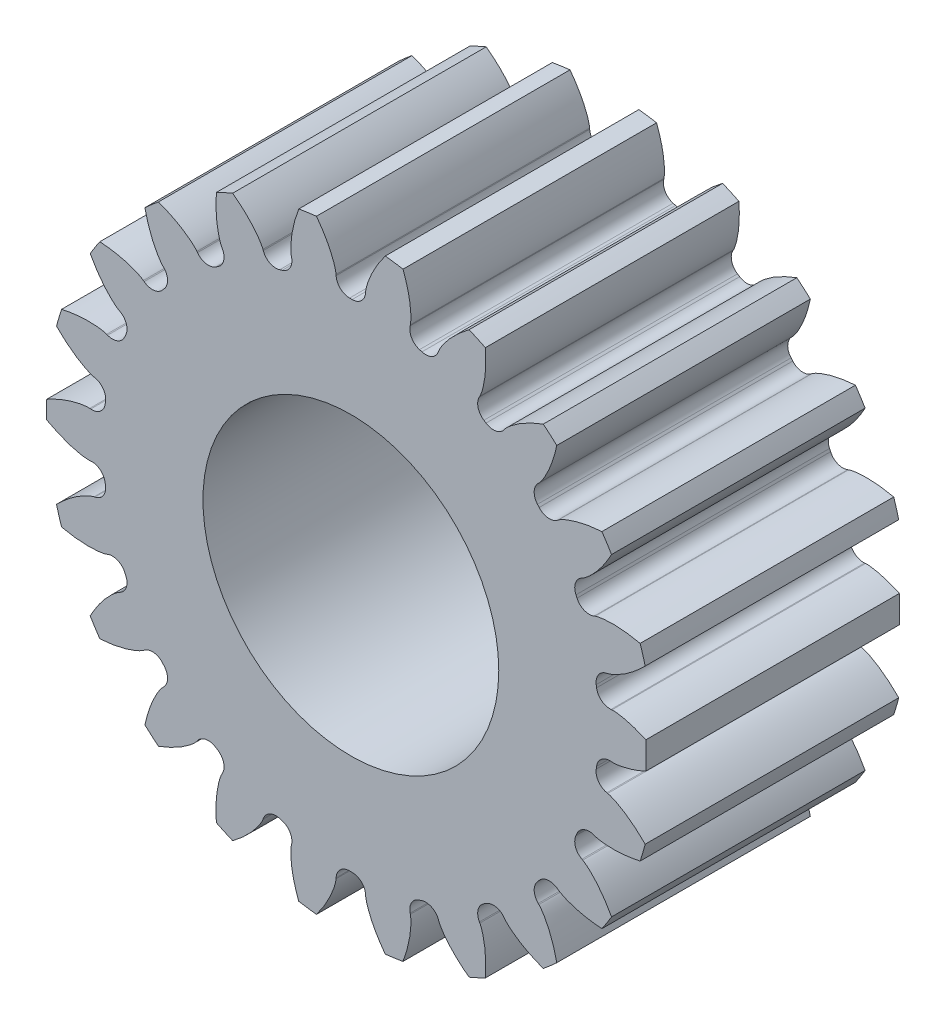
SolidWorks part; units mm, degrees
ref_plane "Front Plane" through (0, 0, 0) normal (0, 0, 1) x (1, 0, 0)
ref_plane "Top Plane" through (0, 0, 0) normal (0, 1, 0) x (1, 0, 0)
ref_plane "Right Plane" through (0, 0, 0) normal (1, 0, 0) x (0, 0, -1)
sketch "Sketch1" plane through (0, 0, 0) normal (0, 0, 1) x (1, 0, 0)
  circle A0 centre (-854.9, 935.5) radius 17.5
  line B0 (-820, 933.8919) -> (-820, 937.1081)
  line B1 (-824.0056, 938.173) -> (-824.1199, 938.1631)
  line B2 (-824.6164, 941.6165) -> (-824.5039, 941.6393)
  line B3 (-826.0101, 946.7687) -> (-826.117, 946.727)
  line B4 (-827.5663, 949.9006) -> (-827.4648, 949.9542)
  line B5 (-830.3551, 954.4514) -> (-830.4459, 954.3814)
  line B6 (-832.7306, 957.0181) -> (-832.6484, 957.098)
  line B7 (-836.6885, 960.5989) -> (-836.756, 960.506)
  line B8 (-839.691, 962.3923) -> (-839.6346, 962.4922)
  line B9 (-844.4974, 964.713) -> (-844.5359, 964.6049)
  line B10 (-847.8835, 965.5878) -> (-847.8575, 965.6996)
  line B11 (-853.149, 966.4604) -> (-853.1556, 966.3458)
  line B12 (-856.6444, 966.3458) -> (-856.651, 966.4604)
  line B13 (-861.9425, 965.6996) -> (-861.9165, 965.5878)
  line B14 (-865.2641, 964.6049) -> (-865.3026, 964.713)
  line B15 (-870.1654, 962.4922) -> (-870.109, 962.3923)
  line B16 (-873.044, 960.506) -> (-873.1115, 960.5989)
  line B17 (-877.1516, 957.098) -> (-877.0694, 957.0181)
  line B18 (-879.3541, 954.3814) -> (-879.4449, 954.4514)
  line B19 (-882.3352, 949.9542) -> (-882.2337, 949.9006)
  line B20 (-883.683, 946.727) -> (-883.7899, 946.7687)
  line B21 (-885.2961, 941.6393) -> (-885.1836, 941.6165)
  line B22 (-885.6801, 938.1631) -> (-885.7944, 938.173)
  line B23 (-885.7944, 932.827) -> (-885.6801, 932.8369)
  line B24 (-885.1836, 929.3835) -> (-885.2961, 929.3607)
  line B25 (-883.7899, 924.2313) -> (-883.683, 924.273)
  line B26 (-882.2337, 921.0994) -> (-882.3352, 921.0458)
  line B27 (-879.4449, 916.5486) -> (-879.3541, 916.6186)
  line B28 (-877.0694, 913.9819) -> (-877.1516, 913.902)
  line B29 (-873.1115, 910.4011) -> (-873.044, 910.494)
  line B30 (-870.109, 908.6077) -> (-870.1654, 908.5078)
  line B31 (-865.3026, 906.287) -> (-865.2641, 906.3951)
  line B32 (-861.9165, 905.4122) -> (-861.9425, 905.3004)
  line B33 (-856.651, 904.5396) -> (-856.6444, 904.6542)
  line B34 (-853.1556, 904.6542) -> (-853.149, 904.5396)
  line B35 (-847.8575, 905.3004) -> (-847.8835, 905.4122)
  line B36 (-844.5359, 906.3951) -> (-844.4974, 906.287)
  line B37 (-839.6346, 908.5078) -> (-839.691, 908.6077)
  line B38 (-836.756, 910.494) -> (-836.6885, 910.4011)
  line B39 (-832.6484, 913.902) -> (-832.7306, 913.9819)
  line B40 (-830.4459, 916.6186) -> (-830.3551, 916.5486)
  line B41 (-827.4648, 921.0458) -> (-827.5663, 921.0994)
  line B42 (-826.117, 924.273) -> (-826.0101, 924.2313)
  line B43 (-824.5039, 929.3607) -> (-824.6164, 929.3835)
  line B44 (-824.1199, 932.8369) -> (-824.0056, 932.827)
  arc B45 (-825.8284, 939.527) -> (-824.1199, 938.1631) centre (-824.2559, 939.7448) ccw
  arc B46 (-825.8284, 939.527) -> (-825.8715, 939.8266) centre (-854.9, 935.5) ccw
  arc B47 (-824.6164, 941.6165) -> (-825.8715, 939.8266) centre (-824.3013, 940.0606) ccw
  arc B48 (-820.0749, 944.622) -> (-820.6715, 946.654) centre (-854.9, 935.5) ccw
  arc B49 (-828.1405, 947.5543) -> (-826.117, 946.727) centre (-826.6931, 948.2063) ccw
  arc B50 (-828.1405, 947.5543) -> (-828.2663, 947.8296) centre (-854.9, 935.5) ccw
  arc B51 (-827.5663, 949.9006) -> (-828.2663, 947.8296) centre (-826.8256, 948.4965) ccw
  arc B52 (-824.0555, 954.0639) -> (-825.2004, 955.8454) centre (-854.9, 935.5) ccw
  arc B53 (-832.6205, 954.605) -> (-830.4459, 954.3814) centre (-831.4154, 955.6384) ccw
  arc B54 (-832.6205, 954.605) -> (-832.8188, 954.8338) centre (-854.9, 935.5) ccw
  arc B55 (-832.7306, 957.0181) -> (-832.8188, 954.8338) centre (-831.6244, 955.8795) ccw
  arc B56 (-830.535, 962.0018) -> (-832.1355, 963.3886) centre (-854.9, 935.5) ccw
  arc B57 (-838.9055, 960.108) -> (-836.756, 960.506) centre (-838.0404, 961.439) ccw
  arc B58 (-838.9055, 960.108) -> (-839.1602, 960.2716) centre (-854.9, 935.5) ccw
  arc B59 (-839.691, 962.3923) -> (-839.1602, 960.2716) centre (-838.3088, 961.6115) ccw
  arc B60 (-838.9883, 967.7927) -> (-840.9147, 968.6725) centre (-854.9, 935.5) ccw
  arc B61 (-846.4863, 963.6173) -> (-844.5359, 964.6049) centre (-846.0312, 965.1382) ccw
  arc B62 (-846.4863, 963.6173) -> (-846.7767, 963.7026) centre (-854.9, 935.5) ccw
  arc B63 (-847.8835, 965.5878) -> (-846.7767, 963.7026) centre (-846.3373, 965.2281) ccw
  arc B64 (-848.7308, 970.9675) -> (-850.827, 971.2688) centre (-854.9, 935.5) ccw
  arc B65 (-854.7487, 964.8488) -> (-853.1556, 966.3458) centre (-854.7405, 966.4363) ccw
  arc B66 (-854.7487, 964.8488) -> (-855.0513, 964.8488) centre (-854.9, 935.5) ccw
  arc B67 (-856.6444, 966.3458) -> (-855.0513, 964.8488) centre (-855.0595, 966.4363) ccw
  arc B68 (-858.973, 971.2688) -> (-861.0692, 970.9675) centre (-854.9, 935.5) ccw
  arc B69 (-863.0233, 963.7026) -> (-861.9165, 965.5878) centre (-863.4627, 965.2281) ccw
  arc B70 (-863.0233, 963.7026) -> (-863.3137, 963.6173) centre (-854.9, 935.5) ccw
  arc B71 (-865.2641, 964.6049) -> (-863.3137, 963.6173) centre (-863.7688, 965.1382) ccw
  arc B72 (-868.8853, 968.6725) -> (-870.8117, 967.7927) centre (-854.9, 935.5) ccw
  arc B73 (-870.6398, 960.2716) -> (-870.109, 962.3923) centre (-871.4912, 961.6115) ccw
  arc B74 (-870.6398, 960.2716) -> (-870.8945, 960.108) centre (-854.9, 935.5) ccw
  arc B75 (-873.044, 960.506) -> (-870.8945, 960.108) centre (-871.7596, 961.439) ccw
  arc B76 (-877.6645, 963.3886) -> (-879.265, 962.0018) centre (-854.9, 935.5) ccw
  arc B77 (-876.9812, 954.8338) -> (-877.0694, 957.0181) centre (-878.1756, 955.8795) ccw
  arc B78 (-876.9812, 954.8338) -> (-877.1795, 954.605) centre (-854.9, 935.5) ccw
  arc B79 (-879.3541, 954.3814) -> (-877.1795, 954.605) centre (-878.3846, 955.6384) ccw
  arc B80 (-884.5996, 955.8454) -> (-885.7445, 954.0639) centre (-854.9, 935.5) ccw
  arc B81 (-881.5337, 947.8296) -> (-882.2337, 949.9006) centre (-882.9744, 948.4965) ccw
  arc B82 (-881.5337, 947.8296) -> (-881.6595, 947.5543) centre (-854.9, 935.5) ccw
  arc B83 (-883.683, 946.727) -> (-881.6595, 947.5543) centre (-883.1069, 948.2063) ccw
  arc B84 (-889.1285, 946.654) -> (-889.7251, 944.622) centre (-854.9, 935.5) ccw
  arc B85 (-883.9285, 939.8266) -> (-885.1836, 941.6165) centre (-885.4987, 940.0606) ccw
  arc B86 (-883.9285, 939.8266) -> (-883.9716, 939.527) centre (-854.9, 935.5) ccw
  arc B87 (-885.6801, 938.1631) -> (-883.9716, 939.527) centre (-885.5441, 939.7448) ccw
  arc B88 (-890.8844, 936.5589) -> (-890.8844, 934.4411) centre (-854.9, 935.5) ccw
  arc B89 (-883.9716, 931.473) -> (-885.6801, 932.8369) centre (-885.5441, 931.2552) ccw
  arc B90 (-883.9716, 931.473) -> (-883.9285, 931.1734) centre (-854.9, 935.5) ccw
  arc B91 (-885.1836, 929.3835) -> (-883.9285, 931.1734) centre (-885.4987, 930.9394) ccw
  arc B92 (-889.7251, 926.378) -> (-889.1285, 924.346) centre (-854.9, 935.5) ccw
  arc B93 (-881.6595, 923.4457) -> (-883.683, 924.273) centre (-883.1069, 922.7937) ccw
  arc B94 (-881.6595, 923.4457) -> (-881.5337, 923.1704) centre (-854.9, 935.5) ccw
  arc B95 (-882.2337, 921.0994) -> (-881.5337, 923.1704) centre (-882.9744, 922.5035) ccw
  arc B96 (-885.7445, 916.9361) -> (-884.5996, 915.1546) centre (-854.9, 935.5) ccw
  arc B97 (-877.1795, 916.395) -> (-879.3541, 916.6186) centre (-878.3846, 915.3616) ccw
  arc B98 (-877.1795, 916.395) -> (-876.9812, 916.1662) centre (-854.9, 935.5) ccw
  arc B99 (-877.0694, 913.9819) -> (-876.9812, 916.1662) centre (-878.1756, 915.1205) ccw
  arc B100 (-879.265, 908.9982) -> (-877.6645, 907.6114) centre (-854.9, 935.5) ccw
  arc B101 (-870.8945, 910.892) -> (-873.044, 910.494) centre (-871.7596, 909.561) ccw
  arc B102 (-870.8945, 910.892) -> (-870.6398, 910.7284) centre (-854.9, 935.5) ccw
  arc B103 (-870.109, 908.6077) -> (-870.6398, 910.7284) centre (-871.4912, 909.3885) ccw
  arc B104 (-870.8117, 903.2073) -> (-868.8853, 902.3275) centre (-854.9, 935.5) ccw
  arc B105 (-863.3137, 907.3827) -> (-865.2641, 906.3951) centre (-863.7688, 905.8618) ccw
  arc B106 (-863.3137, 907.3827) -> (-863.0233, 907.2974) centre (-854.9, 935.5) ccw
  arc B107 (-861.9165, 905.4122) -> (-863.0233, 907.2974) centre (-863.4627, 905.7719) ccw
  arc B108 (-861.0692, 900.0325) -> (-858.973, 899.7312) centre (-854.9, 935.5) ccw
  arc B109 (-855.0513, 906.1512) -> (-856.6444, 904.6542) centre (-855.0595, 904.5637) ccw
  arc B110 (-855.0513, 906.1512) -> (-854.7487, 906.1512) centre (-854.9, 935.5) ccw
  arc B111 (-853.1556, 904.6542) -> (-854.7487, 906.1512) centre (-854.7405, 904.5637) ccw
  arc B112 (-850.827, 899.7312) -> (-848.7308, 900.0325) centre (-854.9, 935.5) ccw
  arc B113 (-846.7767, 907.2974) -> (-847.8835, 905.4122) centre (-846.3373, 905.7719) ccw
  arc B114 (-846.7767, 907.2974) -> (-846.4863, 907.3827) centre (-854.9, 935.5) ccw
  arc B115 (-844.5359, 906.3951) -> (-846.4863, 907.3827) centre (-846.0312, 905.8618) ccw
  arc B116 (-840.9147, 902.3275) -> (-838.9883, 903.2073) centre (-854.9, 935.5) ccw
  arc B117 (-839.1602, 910.7284) -> (-839.691, 908.6077) centre (-838.3088, 909.3885) ccw
  arc B118 (-839.1602, 910.7284) -> (-838.9055, 910.892) centre (-854.9, 935.5) ccw
  arc B119 (-836.756, 910.494) -> (-838.9055, 910.892) centre (-838.0404, 909.561) ccw
  arc B120 (-832.1355, 907.6114) -> (-830.535, 908.9982) centre (-854.9, 935.5) ccw
  arc B121 (-832.8188, 916.1662) -> (-832.7306, 913.9819) centre (-831.6244, 915.1205) ccw
  arc B122 (-832.8188, 916.1662) -> (-832.6205, 916.395) centre (-854.9, 935.5) ccw
  arc B123 (-830.4459, 916.6186) -> (-832.6205, 916.395) centre (-831.4154, 915.3616) ccw
  arc B124 (-825.2004, 915.1546) -> (-824.0555, 916.9361) centre (-854.9, 935.5) ccw
  arc B125 (-828.2663, 923.1704) -> (-827.5663, 921.0994) centre (-826.8256, 922.5035) ccw
  arc B126 (-828.2663, 923.1704) -> (-828.1405, 923.4457) centre (-854.9, 935.5) ccw
  arc B127 (-826.117, 924.273) -> (-828.1405, 923.4457) centre (-826.6931, 922.7937) ccw
  arc B128 (-820.6715, 924.346) -> (-820.0749, 926.378) centre (-854.9, 935.5) ccw
  arc B129 (-825.8715, 931.1734) -> (-824.6164, 929.3835) centre (-824.3013, 930.9394) ccw
  arc B130 (-825.8715, 931.1734) -> (-825.8284, 931.473) centre (-854.9, 935.5) ccw
  arc B131 (-824.1199, 932.8369) -> (-825.8284, 931.473) centre (-824.2559, 931.2552) ccw
  spline B132 degree 5 poles (-820, 937.1081) (-820.1692, 937.1862) (-820.3965, 937.2872) (-820.6825, 937.4075) (-821.0423, 937.5478) (-821.4475, 937.6893) (-821.7108, 937.7744) (-821.9745, 937.8529) (-822.1948, 937.9129) (-822.4005, 937.9653) (-822.5771, 938.0061) (-822.7833, 938.049) (-822.9454, 938.0799) (-823.1223, 938.1098) (-823.2845, 938.1327) (-823.4466, 938.15) (-823.6087, 938.165) (-823.756, 938.177) (-823.8736, 938.1805) (-823.947, 938.178) (-824.0056, 938.173) knots 0 0 0 0 0 0 0.168282 0.225425 0.282568 0.353997 0.396854 0.425425 0.482568 0.496854 0.553997 0.568282 0.625425 0.639711 0.668282 0.711139 0.725425 0.782568 0.782568 0.782568 0.782568 0.782568 0.782568 weights 1 1 1 1 1 1 1 1 1 1 1 1 1 1 1 1 1 1 1 1 1
  spline B133 degree 5 poles (-824.5039, 941.6393) (-824.4463, 941.651) (-824.3752, 941.6692) (-824.2773, 941.7011) (-824.153, 941.748) (-824.0154, 941.8024) (-823.8781, 941.8581) (-823.7418, 941.9173) (-823.5799, 941.9938) (-823.4194, 942.0748) (-823.2333, 942.173) (-823.0486, 942.2753) (-822.8527, 942.3909) (-822.6583, 942.5105) (-822.4143, 942.668) (-822.1478, 942.8502) (-821.8719, 943.0492) (-821.5505, 943.2953) (-821.222, 943.5624) (-820.9106, 943.8299) (-820.6159, 944.0964) (-820.3837, 944.3165) (-820.2229, 944.4738) (-820.1203, 944.5762) (-820.0749, 944.622) knots 0 0 0 0 0 0 0.057143 0.071429 0.1 0.128571 0.142857 0.2 0.214286 0.271429 0.3 0.342857 0.4 0.428571 0.485714 0.571429 0.642857 0.714286 0.8 0.871429 0.942857 1 1 1 1 1 1 weights 1 1 1 1 1 1 1 1 1 1 1 1 1 1 1 1 1 1 1 1 1 1 1 1 1
  spline B134 degree 5 poles (-820.6715, 946.654) (-820.8763, 946.6993) (-821.1437, 946.7544) (-821.4737, 946.8159) (-821.8812, 946.8814) (-822.3653, 946.9432) (-822.7078, 946.9788) (-823.0644, 947.0072) (-823.404, 947.0249) (-823.6959, 947.0328) (-823.9711, 947.0338) (-824.1994, 947.0293) (-824.4115, 947.0216) (-824.5925, 947.011) (-824.8024, 946.9941) (-824.9666, 946.9781) (-825.1448, 946.9569) (-825.3068, 946.9332) (-825.4673, 946.9041) (-825.6271, 946.8728) (-825.7718, 946.8429) (-825.8856, 946.8131) (-825.9553, 946.79) (-826.0101, 946.7687) knots 0 0 0 0 0 0 0.185714 0.242857 0.3 0.371429 0.442857 0.5 0.571429 0.614286 0.642857 0.7 0.714286 0.771429 0.785714 0.842857 0.857143 0.885714 0.928571 0.942857 1 1 1 1 1 1 weights 1 1 1 1 1 1 1 1 1 1 1 1 1 1 1 1 1 1 1 1 1 1 1 1
  spline B135 degree 5 poles (-827.4648, 949.9542) (-827.4128, 949.9816) (-827.3497, 950.0191) (-827.2648, 950.0773) (-827.1587, 950.1574) (-827.042, 950.2483) (-826.926, 950.3404) (-826.8119, 950.4357) (-826.6781, 950.5547) (-826.5469, 950.6776) (-826.396, 950.8242) (-826.2476, 950.9744) (-826.0922, 951.1405) (-825.9394, 951.3101) (-825.7497, 951.53) (-825.5453, 951.7799) (-825.3366, 952.0485) (-825.0975, 952.3751) (-824.8576, 952.724) (-824.6342, 953.0684) (-824.4265, 953.4071) (-824.2657, 953.6837) (-824.1558, 953.8799) (-824.0862, 954.0071) (-824.0555, 954.0639) knots 0 0 0 0 0 0 0.057143 0.071429 0.1 0.128571 0.142857 0.2 0.214286 0.271429 0.3 0.342857 0.4 0.428571 0.485714 0.571429 0.642857 0.714286 0.8 0.871429 0.942857 1 1 1 1 1 1 weights 1 1 1 1 1 1 1 1 1 1 1 1 1 1 1 1 1 1 1 1 1 1 1 1 1
  spline B136 degree 5 poles (-825.2004, 955.8454) (-825.4097, 955.8312) (-825.6818, 955.8088) (-826.0158, 955.7748) (-826.4252, 955.7228) (-826.9071, 955.6458) (-827.2457, 955.5835) (-827.596, 955.5102) (-827.9268, 955.4315) (-828.2091, 955.3568) (-828.4734, 955.2802) (-828.6911, 955.2117) (-828.8926, 955.1445) (-829.0631, 955.0833) (-829.2598, 955.008) (-829.4129, 954.9463) (-829.5779, 954.8759) (-829.7267, 954.8074) (-829.8724, 954.7343) (-830.0169, 954.6593) (-830.1473, 954.5898) (-830.2481, 954.5291) (-830.3085, 954.4874) (-830.3551, 954.4514) knots 0 0 0 0 0 0 0.185714 0.242857 0.3 0.371429 0.442857 0.5 0.571429 0.614286 0.642857 0.7 0.714286 0.771429 0.785714 0.842857 0.857143 0.885714 0.928571 0.942857 1 1 1 1 1 1 weights 1 1 1 1 1 1 1 1 1 1 1 1 1 1 1 1 1 1 1 1 1 1 1 1
  spline B137 degree 5 poles (-832.6484, 957.098) (-832.6062, 957.139) (-832.5562, 957.1928) (-832.4912, 957.2726) (-832.4119, 957.3793) (-832.3256, 957.4994) (-832.2402, 957.6205) (-832.1576, 957.744) (-832.0627, 957.8959) (-831.9714, 958.0508) (-831.8679, 958.234) (-831.7678, 958.4199) (-831.6656, 958.6231) (-831.5667, 958.8288) (-831.4466, 959.0932) (-831.3209, 959.3906) (-831.1963, 959.7071) (-831.059, 960.0879) (-830.9271, 960.4902) (-830.8098, 960.8836) (-830.7059, 961.2672) (-830.6296, 961.5778) (-830.5794, 961.7971) (-830.5485, 961.9387) (-830.535, 962.0018) knots 0 0 0 0 0 0 0.057143 0.071429 0.1 0.128571 0.142857 0.2 0.214286 0.271429 0.3 0.342857 0.4 0.428571 0.485714 0.571429 0.642857 0.714286 0.8 0.871429 0.942857 1 1 1 1 1 1 weights 1 1 1 1 1 1 1 1 1 1 1 1 1 1 1 1 1 1 1 1 1 1 1 1 1
  spline B138 degree 5 poles (-832.1355, 963.3886) (-832.3322, 963.3161) (-832.587, 963.2179) (-832.8978, 963.0912) (-833.2761, 962.9259) (-833.7168, 962.7162) (-834.0241, 962.5611) (-834.3395, 962.3921) (-834.6347, 962.2234) (-834.8845, 962.0722) (-835.1166, 961.9242) (-835.3062, 961.7971) (-835.4805, 961.6759) (-835.627, 961.5691) (-835.7945, 961.4415) (-835.9239, 961.3392) (-836.0624, 961.2251) (-836.1859, 961.1175) (-836.3051, 961.0062) (-836.4226, 960.8935) (-836.5282, 960.7901) (-836.6078, 960.7036) (-836.654, 960.6465) (-836.6885, 960.5989) knots 0 0 0 0 0 0 0.185714 0.242857 0.3 0.371429 0.442857 0.5 0.571429 0.614286 0.642857 0.7 0.714286 0.771429 0.785714 0.842857 0.857143 0.885714 0.928571 0.942857 1 1 1 1 1 1 weights 1 1 1 1 1 1 1 1 1 1 1 1 1 1 1 1 1 1 1 1 1 1 1 1
  spline B139 degree 5 poles (-839.6346, 962.4922) (-839.6056, 962.5434) (-839.5729, 962.6091) (-839.5329, 962.7039) (-839.487, 962.8286) (-839.4379, 962.9683) (-839.3901, 963.1084) (-839.3457, 963.2502) (-839.2974, 963.4227) (-839.2535, 963.5971) (-839.2058, 963.802) (-839.1622, 964.0086) (-839.1213, 964.2323) (-839.0844, 964.4576) (-839.0436, 964.7451) (-839.0068, 965.0659) (-838.9765, 965.4047) (-838.952, 965.8087) (-838.9387, 966.2319) (-838.937, 966.6424) (-838.9454, 967.0397) (-838.9597, 967.3593) (-838.9733, 967.5837) (-838.9835, 967.7284) (-838.9883, 967.7927) knots 0 0 0 0 0 0 0.057143 0.071429 0.1 0.128571 0.142857 0.2 0.214286 0.271429 0.3 0.342857 0.4 0.428571 0.485714 0.571429 0.642857 0.714286 0.8 0.871429 0.942857 1 1 1 1 1 1 weights 1 1 1 1 1 1 1 1 1 1 1 1 1 1 1 1 1 1 1 1 1 1 1 1 1
  spline B140 degree 5 poles (-840.9147, 968.6725) (-841.083, 968.5474) (-841.2999, 968.3814) (-841.5624, 968.1723) (-841.8788, 967.9071) (-842.2425, 967.5818) (-842.4937, 967.3463) (-842.7487, 967.0953) (-842.9845, 966.8503) (-843.1815, 966.6348) (-843.3625, 966.4275) (-843.5086, 966.2521) (-843.6417, 966.0867) (-843.7522, 965.943) (-843.8769, 965.7733) (-843.9723, 965.6387) (-844.073, 965.4902) (-844.1612, 965.3522) (-844.2443, 965.2118) (-844.3253, 965.0706) (-844.3974, 964.9416) (-844.4495, 964.8361) (-844.4776, 964.7684) (-844.4974, 964.713) knots 0 0 0 0 0 0 0.185714 0.242857 0.3 0.371429 0.442857 0.5 0.571429 0.614286 0.642857 0.7 0.714286 0.771429 0.785714 0.842857 0.857143 0.885714 0.928571 0.942857 1 1 1 1 1 1 weights 1 1 1 1 1 1 1 1 1 1 1 1 1 1 1 1 1 1 1 1 1 1 1 1
  spline B141 degree 5 poles (-847.8575, 965.6996) (-847.8442, 965.7569) (-847.8312, 965.8291) (-847.8196, 965.9314) (-847.8107, 966.064) (-847.803, 966.2118) (-847.7966, 966.3598) (-847.7939, 966.5083) (-847.7962, 966.6874) (-847.8031, 966.8671) (-847.8151, 967.0771) (-847.8314, 967.2877) (-847.8552, 967.5138) (-847.8833, 967.7404) (-847.9252, 968.0277) (-847.9802, 968.3459) (-848.0466, 968.6795) (-848.1369, 969.0741) (-848.2434, 969.4838) (-848.3574, 969.8782) (-848.4774, 970.257) (-848.5812, 970.5597) (-848.6575, 970.7712) (-848.708, 970.9071) (-848.7308, 970.9675) knots 0 0 0 0 0 0 0.057143 0.071429 0.1 0.128571 0.142857 0.2 0.214286 0.271429 0.3 0.342857 0.4 0.428571 0.485714 0.571429 0.642857 0.714286 0.8 0.871429 0.942857 1 1 1 1 1 1 weights 1 1 1 1 1 1 1 1 1 1 1 1 1 1 1 1 1 1 1 1 1 1 1 1 1
  spline B142 degree 5 poles (-850.827, 971.2688) (-850.9533, 971.1014) (-851.1145, 970.8811) (-851.3075, 970.6064) (-851.5364, 970.2629) (-851.7937, 969.8483) (-851.9684, 969.5516) (-852.1424, 969.2389) (-852.2995, 968.9374) (-852.4279, 968.6751) (-852.5432, 968.4252) (-852.6339, 968.2157) (-852.715, 968.0195) (-852.7805, 967.8505) (-852.8524, 967.6526) (-852.906, 967.4965) (-852.9608, 967.3257) (-853.0066, 967.1684) (-853.0467, 967.0104) (-853.0846, 966.852) (-853.1175, 966.708) (-853.1377, 966.5921) (-853.1457, 966.5191) (-853.149, 966.4604) knots 0 0 0 0 0 0 0.185714 0.242857 0.3 0.371429 0.442857 0.5 0.571429 0.614286 0.642857 0.7 0.714286 0.771429 0.785714 0.842857 0.857143 0.885714 0.928571 0.942857 1 1 1 1 1 1 weights 1 1 1 1 1 1 1 1 1 1 1 1 1 1 1 1 1 1 1 1 1 1 1 1
  spline B143 degree 5 poles (-856.651, 966.4604) (-856.6543, 966.5191) (-856.6623, 966.5921) (-856.68, 966.6935) (-856.7087, 966.8232) (-856.7429, 966.9672) (-856.7785, 967.111) (-856.8178, 967.2543) (-856.8704, 967.4255) (-856.9277, 967.5959) (-856.9984, 967.7941) (-857.0734, 967.9915) (-857.1599, 968.2018) (-857.2507, 968.4112) (-857.3719, 968.6752) (-857.5143, 968.9649) (-857.6719, 969.2663) (-857.8698, 969.6195) (-858.0874, 969.9826) (-858.3079, 970.3289) (-858.5298, 970.6586) (-858.7146, 970.9197) (-858.8474, 971.1012) (-858.9342, 971.2173) (-858.973, 971.2688) knots 0 0 0 0 0 0 0.057143 0.071429 0.1 0.128571 0.142857 0.2 0.214286 0.271429 0.3 0.342857 0.4 0.428571 0.485714 0.571429 0.642857 0.714286 0.8 0.871429 0.942857 1 1 1 1 1 1 weights 1 1 1 1 1 1 1 1 1 1 1 1 1 1 1 1 1 1 1 1 1 1 1 1 1
  spline B144 degree 5 poles (-861.0692, 970.9675) (-861.1432, 970.7713) (-861.2359, 970.5144) (-861.3437, 970.1965) (-861.4665, 969.8024) (-861.5966, 969.3321) (-861.6806, 968.9982) (-861.7594, 968.6492) (-861.8253, 968.3156) (-861.8746, 968.0277) (-861.9147, 967.7555) (-861.9428, 967.5289) (-861.9654, 967.3178) (-861.9806, 967.1372) (-861.9938, 966.9271) (-862.0013, 966.7622) (-862.0057, 966.5829) (-862.0053, 966.4191) (-861.9993, 966.2561) (-861.9911, 966.0935) (-861.982, 965.946) (-861.9688, 965.8291) (-861.9558, 965.7569) (-861.9425, 965.6996) knots 0 0 0 0 0 0 0.185714 0.242857 0.3 0.371429 0.442857 0.5 0.571429 0.614286 0.642857 0.7 0.714286 0.771429 0.785714 0.842857 0.857143 0.885714 0.928571 0.942857 1 1 1 1 1 1 weights 1 1 1 1 1 1 1 1 1 1 1 1 1 1 1 1 1 1 1 1 1 1 1 1
  spline B145 degree 5 poles (-865.3026, 964.713) (-865.3224, 964.7684) (-865.3505, 964.8361) (-865.3961, 964.9285) (-865.4602, 965.0448) (-865.5336, 965.1733) (-865.6082, 965.3013) (-865.6863, 965.4277) (-865.7851, 965.5771) (-865.8881, 965.7245) (-866.0117, 965.8948) (-866.1392, 966.063) (-866.2816, 966.2404) (-866.4277, 966.4158) (-866.6183, 966.6349) (-866.8366, 966.8728) (-867.0727, 967.1176) (-867.362, 967.4007) (-867.6732, 967.6878) (-867.9823, 967.958) (-868.288, 968.2118) (-868.5389, 968.4103) (-868.7175, 968.547) (-868.8335, 968.634) (-868.8853, 968.6725) knots 0 0 0 0 0 0 0.057143 0.071429 0.1 0.128571 0.142857 0.2 0.214286 0.271429 0.3 0.342857 0.4 0.428571 0.485714 0.571429 0.642857 0.714286 0.8 0.871429 0.942857 1 1 1 1 1 1 weights 1 1 1 1 1 1 1 1 1 1 1 1 1 1 1 1 1 1 1 1 1 1 1 1 1
  spline B146 degree 5 poles (-870.8117, 967.7927) (-870.8274, 967.5836) (-870.8439, 967.311) (-870.8578, 966.9757) (-870.8646, 966.5629) (-870.8569, 966.075) (-870.8434, 965.731) (-870.8208, 965.3739) (-870.7899, 965.0352) (-870.7562, 964.7452) (-870.718, 964.4726) (-870.6811, 964.2474) (-870.6433, 964.0384) (-870.607, 963.8609) (-870.5605, 963.6555) (-870.5212, 963.4952) (-870.4749, 963.3219) (-870.4284, 963.1648) (-870.3767, 963.0102) (-870.323, 962.8565) (-870.2728, 962.7175) (-870.2271, 962.6091) (-870.1944, 962.5434) (-870.1654, 962.4922) knots 0 0 0 0 0 0 0.185714 0.242857 0.3 0.371429 0.442857 0.5 0.571429 0.614286 0.642857 0.7 0.714286 0.771429 0.785714 0.842857 0.857143 0.885714 0.928571 0.942857 1 1 1 1 1 1 weights 1 1 1 1 1 1 1 1 1 1 1 1 1 1 1 1 1 1 1 1 1 1 1 1
  spline B147 degree 5 poles (-873.1115, 960.5989) (-873.146, 960.6465) (-873.1922, 960.7036) (-873.2619, 960.7793) (-873.3562, 960.8729) (-873.4628, 960.9755) (-873.5705, 961.0773) (-873.681, 961.1766) (-873.8178, 961.2921) (-873.9582, 961.4045) (-874.1248, 961.533) (-874.2946, 961.6585) (-874.4811, 961.7887) (-874.6707, 961.9158) (-874.9153, 962.0723) (-875.1918, 962.2391) (-875.4874, 962.4074) (-875.8447, 962.5975) (-876.2241, 962.7854) (-876.5968, 962.9575) (-876.9617, 963.1149) (-877.2584, 963.2346) (-877.4682, 963.3155) (-877.604, 963.3663) (-877.6645, 963.3886) knots 0 0 0 0 0 0 0.057143 0.071429 0.1 0.128571 0.142857 0.2 0.214286 0.271429 0.3 0.342857 0.4 0.428571 0.485714 0.571429 0.642857 0.714286 0.8 0.871429 0.942857 1 1 1 1 1 1 weights 1 1 1 1 1 1 1 1 1 1 1 1 1 1 1 1 1 1 1 1 1 1 1 1 1
  spline B148 degree 5 poles (-879.265, 962.0018) (-879.2212, 961.7967) (-879.1603, 961.5305) (-879.0791, 961.2048) (-878.9694, 960.8069) (-878.8245, 960.3409) (-878.7147, 960.0146) (-878.5923, 959.6784) (-878.4673, 959.3621) (-878.3532, 959.0933) (-878.2398, 958.8426) (-878.1409, 958.6368) (-878.0458, 958.447) (-877.9609, 958.2869) (-877.8584, 958.1029) (-877.7756, 957.9602) (-877.6824, 957.8069) (-877.5935, 957.6694) (-877.5003, 957.5355) (-877.4055, 957.4032) (-877.3181, 957.284) (-877.2438, 957.1928) (-877.1938, 957.139) (-877.1516, 957.098) knots 0 0 0 0 0 0 0.185714 0.242857 0.3 0.371429 0.442857 0.5 0.571429 0.614286 0.642857 0.7 0.714286 0.771429 0.785714 0.842857 0.857143 0.885714 0.928571 0.942857 1 1 1 1 1 1 weights 1 1 1 1 1 1 1 1 1 1 1 1 1 1 1 1 1 1 1 1 1 1 1 1
  spline B149 degree 5 poles (-879.4449, 954.4514) (-879.4915, 954.4874) (-879.5519, 954.5291) (-879.6401, 954.5822) (-879.757, 954.6454) (-879.8882, 954.7138) (-880.0201, 954.7811) (-880.1542, 954.8453) (-880.318, 954.9176) (-880.4844, 954.9859) (-880.6804, 955.0623) (-880.8787, 955.1349) (-881.0943, 955.2072) (-881.312, 955.2757) (-881.5908, 955.357) (-881.9031, 955.4391) (-882.2341, 955.5173) (-882.6306, 955.5991) (-883.0475, 955.6724) (-883.4536, 955.7326) (-883.8481, 955.7808) (-884.1664, 955.8121) (-884.3906, 955.8306) (-884.5352, 955.8411) (-884.5996, 955.8454) knots 0 0 0 0 0 0 0.057143 0.071429 0.1 0.128571 0.142857 0.2 0.214286 0.271429 0.3 0.342857 0.4 0.428571 0.485714 0.571429 0.642857 0.714286 0.8 0.871429 0.942857 1 1 1 1 1 1 weights 1 1 1 1 1 1 1 1 1 1 1 1 1 1 1 1 1 1 1 1 1 1 1 1 1
  spline B150 degree 5 poles (-885.7445, 954.0639) (-885.6447, 953.8795) (-885.5112, 953.6412) (-885.3416, 953.3516) (-885.1242, 953.0007) (-884.8539, 952.5943) (-884.6566, 952.3122) (-884.4444, 952.0241) (-884.2354, 951.7559) (-884.0502, 951.5301) (-883.8707, 951.3215) (-883.7179, 951.1519) (-883.5731, 950.9966) (-883.4466, 950.8668) (-883.2964, 950.7192) (-883.1767, 950.6056) (-883.0441, 950.4848) (-882.92, 950.3779) (-882.793, 950.2757) (-882.6647, 950.1754) (-882.5473, 950.0857) (-882.4503, 950.0191) (-882.3872, 949.9816) (-882.3352, 949.9542) knots 0 0 0 0 0 0 0.185714 0.242857 0.3 0.371429 0.442857 0.5 0.571429 0.614286 0.642857 0.7 0.714286 0.771429 0.785714 0.842857 0.857143 0.885714 0.928571 0.942857 1 1 1 1 1 1 weights 1 1 1 1 1 1 1 1 1 1 1 1 1 1 1 1 1 1 1 1 1 1 1 1
  spline B151 degree 5 poles (-883.7899, 946.7687) (-883.8447, 946.79) (-883.9144, 946.8131) (-884.014, 946.8391) (-884.144, 946.8669) (-884.2891, 946.8955) (-884.4347, 946.9229) (-884.5814, 946.9468) (-884.759, 946.97) (-884.9378, 946.9886) (-885.1474, 947.0067) (-885.3581, 947.0205) (-885.5854, 947.0291) (-885.8136, 947.0335) (-886.104, 947.033) (-886.4268, 947.0238) (-886.7664, 947.0056) (-887.1698, 946.9723) (-887.5906, 946.9252) (-887.9972, 946.8685) (-888.3892, 946.8037) (-888.7035, 946.744) (-888.9238, 946.6986) (-889.0655, 946.6679) (-889.1285, 946.654) knots 0 0 0 0 0 0 0.057143 0.071429 0.1 0.128571 0.142857 0.2 0.214286 0.271429 0.3 0.342857 0.4 0.428571 0.485714 0.571429 0.642857 0.714286 0.8 0.871429 0.942857 1 1 1 1 1 1 weights 1 1 1 1 1 1 1 1 1 1 1 1 1 1 1 1 1 1 1 1 1 1 1 1 1
  spline B152 degree 5 poles (-889.7251, 944.622) (-889.5774, 944.4732) (-889.3822, 944.2822) (-889.1378, 944.0521) (-888.8304, 943.7767) (-888.4566, 943.4629) (-888.1878, 943.2478) (-887.903, 943.0311) (-887.6269, 942.8326) (-887.3856, 942.6682) (-887.1546, 942.5186) (-886.9602, 942.3989) (-886.7776, 942.2907) (-886.6196, 942.2019) (-886.4339, 942.1025) (-886.2871, 942.0273) (-886.1258, 941.9487) (-885.9766, 941.881) (-885.8259, 941.8188) (-885.6746, 941.7587) (-885.5366, 941.7057) (-885.4248, 941.6692) (-885.3537, 941.651) (-885.2961, 941.6393) knots 0 0 0 0 0 0 0.185714 0.242857 0.3 0.371429 0.442857 0.5 0.571429 0.614286 0.642857 0.7 0.714286 0.771429 0.785714 0.842857 0.857143 0.885714 0.928571 0.942857 1 1 1 1 1 1 weights 1 1 1 1 1 1 1 1 1 1 1 1 1 1 1 1 1 1 1 1 1 1 1 1
  spline B153 degree 5 poles (-885.7944, 938.173) (-885.853, 938.178) (-885.9264, 938.1805) (-886.0293, 938.1775) (-886.1618, 938.1675) (-886.3092, 938.1541) (-886.4566, 938.1393) (-886.604, 938.1209) (-886.7809, 938.0931) (-886.9578, 938.0606) (-887.164, 938.0189) (-887.3701, 937.9728) (-887.5906, 937.917) (-887.8108, 937.857) (-888.0893, 937.7746) (-888.3963, 937.6749) (-888.7171, 937.5617) (-889.0948, 937.4162) (-889.4852, 937.2524) (-889.8594, 937.0835) (-890.2173, 936.9108) (-890.5021, 936.765) (-890.7006, 936.6594) (-890.8279, 936.59) (-890.8844, 936.5589) knots 0 0 0 0 0 0 0.057143 0.071429 0.1 0.128571 0.142857 0.2 0.214286 0.271429 0.3 0.342857 0.4 0.428571 0.485714 0.571429 0.642857 0.714286 0.8 0.871429 0.942857 1 1 1 1 1 1 weights 1 1 1 1 1 1 1 1 1 1 1 1 1 1 1 1 1 1 1 1 1 1 1 1 1
  spline B154 degree 5 poles (-890.8844, 934.4411) (-890.7007, 934.34) (-890.4597, 934.2117) (-890.1604, 934.0598) (-889.7878, 933.8821) (-889.3407, 933.6864) (-889.0222, 933.5557) (-888.688, 933.428) (-888.3671, 933.3154) (-888.0892, 933.2256) (-887.8255, 933.1471) (-887.6052, 933.0871) (-887.3995, 933.0347) (-887.2229, 932.9939) (-887.0167, 932.951) (-886.8546, 932.9201) (-886.6777, 932.8902) (-886.5155, 932.8673) (-886.3534, 932.85) (-886.1913, 932.835) (-886.044, 932.823) (-885.9264, 932.8195) (-885.853, 932.822) (-885.7944, 932.827) knots 0 0 0 0 0 0 0.185714 0.242857 0.3 0.371429 0.442857 0.5 0.571429 0.614286 0.642857 0.7 0.714286 0.771429 0.785714 0.842857 0.857143 0.885714 0.928571 0.942857 1 1 1 1 1 1 weights 1 1 1 1 1 1 1 1 1 1 1 1 1 1 1 1 1 1 1 1 1 1 1 1
  spline B155 degree 5 poles (-885.2961, 929.3607) (-885.3537, 929.349) (-885.4248, 929.3308) (-885.5227, 929.2989) (-885.647, 929.252) (-885.7846, 929.1976) (-885.9219, 929.1419) (-886.0582, 929.0827) (-886.2201, 929.0062) (-886.3806, 928.9252) (-886.5667, 928.827) (-886.7514, 928.7247) (-886.9473, 928.6091) (-887.1417, 928.4895) (-887.3857, 928.332) (-887.6522, 928.1498) (-887.9281, 927.9508) (-888.2495, 927.7047) (-888.578, 927.4376) (-888.8894, 927.1701) (-889.1841, 926.9036) (-889.4163, 926.6835) (-889.5771, 926.5262) (-889.6797, 926.4238) (-889.7251, 926.378) knots 0 0 0 0 0 0 0.057143 0.071429 0.1 0.128571 0.142857 0.2 0.214286 0.271429 0.3 0.342857 0.4 0.428571 0.485714 0.571429 0.642857 0.714286 0.8 0.871429 0.942857 1 1 1 1 1 1 weights 1 1 1 1 1 1 1 1 1 1 1 1 1 1 1 1 1 1 1 1 1 1 1 1 1
  spline B156 degree 5 poles (-889.1285, 924.346) (-888.9237, 924.3007) (-888.6563, 924.2456) (-888.3263, 924.1841) (-887.9188, 924.1186) (-887.4347, 924.0568) (-887.0922, 924.0212) (-886.7356, 923.9928) (-886.396, 923.9751) (-886.1041, 923.9672) (-885.8289, 923.9662) (-885.6006, 923.9707) (-885.3885, 923.9784) (-885.2075, 923.989) (-884.9976, 924.0059) (-884.8334, 924.0219) (-884.6552, 924.0431) (-884.4932, 924.0668) (-884.3327, 924.0959) (-884.1729, 924.1272) (-884.0282, 924.1571) (-883.9144, 924.1869) (-883.8447, 924.21) (-883.7899, 924.2313) knots 0 0 0 0 0 0 0.185714 0.242857 0.3 0.371429 0.442857 0.5 0.571429 0.614286 0.642857 0.7 0.714286 0.771429 0.785714 0.842857 0.857143 0.885714 0.928571 0.942857 1 1 1 1 1 1 weights 1 1 1 1 1 1 1 1 1 1 1 1 1 1 1 1 1 1 1 1 1 1 1 1
  spline B157 degree 5 poles (-882.3352, 921.0458) (-882.3872, 921.0184) (-882.4503, 920.9809) (-882.5352, 920.9227) (-882.6413, 920.8426) (-882.758, 920.7517) (-882.874, 920.6596) (-882.9881, 920.5643) (-883.1219, 920.4453) (-883.2531, 920.3224) (-883.404, 920.1758) (-883.5524, 920.0256) (-883.7078, 919.8595) (-883.8606, 919.6899) (-884.0503, 919.47) (-884.2547, 919.2201) (-884.4634, 918.9515) (-884.7025, 918.6249) (-884.9424, 918.276) (-885.1658, 917.9316) (-885.3735, 917.5929) (-885.5343, 917.3163) (-885.6442, 917.1201) (-885.7138, 916.9929) (-885.7445, 916.9361) knots 0 0 0 0 0 0 0.057143 0.071429 0.1 0.128571 0.142857 0.2 0.214286 0.271429 0.3 0.342857 0.4 0.428571 0.485714 0.571429 0.642857 0.714286 0.8 0.871429 0.942857 1 1 1 1 1 1 weights 1 1 1 1 1 1 1 1 1 1 1 1 1 1 1 1 1 1 1 1 1 1 1 1 1
  spline B158 degree 5 poles (-884.5996, 915.1546) (-884.3903, 915.1688) (-884.1182, 915.1912) (-883.7842, 915.2252) (-883.3748, 915.2772) (-882.8929, 915.3542) (-882.5543, 915.4165) (-882.204, 915.4898) (-881.8732, 915.5685) (-881.5909, 915.6432) (-881.3266, 915.7198) (-881.1089, 915.7883) (-880.9074, 915.8555) (-880.7369, 915.9167) (-880.5402, 915.992) (-880.3871, 916.0537) (-880.2221, 916.1241) (-880.0733, 916.1926) (-879.9276, 916.2657) (-879.7831, 916.3407) (-879.6527, 916.4102) (-879.5519, 916.4709) (-879.4915, 916.5126) (-879.4449, 916.5486) knots 0 0 0 0 0 0 0.185714 0.242857 0.3 0.371429 0.442857 0.5 0.571429 0.614286 0.642857 0.7 0.714286 0.771429 0.785714 0.842857 0.857143 0.885714 0.928571 0.942857 1 1 1 1 1 1 weights 1 1 1 1 1 1 1 1 1 1 1 1 1 1 1 1 1 1 1 1 1 1 1 1
  spline B159 degree 5 poles (-877.1516, 913.902) (-877.1938, 913.861) (-877.2438, 913.8072) (-877.3088, 913.7274) (-877.3881, 913.6207) (-877.4744, 913.5006) (-877.5598, 913.3795) (-877.6424, 913.256) (-877.7373, 913.1041) (-877.8286, 912.9492) (-877.9321, 912.766) (-878.0322, 912.5801) (-878.1344, 912.3769) (-878.2333, 912.1712) (-878.3534, 911.9068) (-878.4791, 911.6094) (-878.6037, 911.2929) (-878.741, 910.9121) (-878.8729, 910.5098) (-878.9902, 910.1164) (-879.0941, 909.7328) (-879.1704, 909.4222) (-879.2206, 909.2029) (-879.2515, 909.0613) (-879.265, 908.9982) knots 0 0 0 0 0 0 0.057143 0.071429 0.1 0.128571 0.142857 0.2 0.214286 0.271429 0.3 0.342857 0.4 0.428571 0.485714 0.571429 0.642857 0.714286 0.8 0.871429 0.942857 1 1 1 1 1 1 weights 1 1 1 1 1 1 1 1 1 1 1 1 1 1 1 1 1 1 1 1 1 1 1 1 1
  spline B160 degree 5 poles (-877.6645, 907.6114) (-877.4678, 907.6839) (-877.213, 907.7821) (-876.9022, 907.9088) (-876.5239, 908.0741) (-876.0832, 908.2838) (-875.7759, 908.4389) (-875.4605, 908.6079) (-875.1653, 908.7766) (-874.9155, 908.9278) (-874.6834, 909.0758) (-874.4938, 909.2029) (-874.3195, 909.3241) (-874.173, 909.4309) (-874.0055, 909.5585) (-873.8761, 909.6608) (-873.7376, 909.7749) (-873.6141, 909.8825) (-873.4949, 909.9938) (-873.3774, 910.1065) (-873.2718, 910.2099) (-873.1922, 910.2964) (-873.146, 910.3535) (-873.1115, 910.4011) knots 0 0 0 0 0 0 0.185714 0.242857 0.3 0.371429 0.442857 0.5 0.571429 0.614286 0.642857 0.7 0.714286 0.771429 0.785714 0.842857 0.857143 0.885714 0.928571 0.942857 1 1 1 1 1 1 weights 1 1 1 1 1 1 1 1 1 1 1 1 1 1 1 1 1 1 1 1 1 1 1 1
  spline B161 degree 5 poles (-870.1654, 908.5078) (-870.1944, 908.4566) (-870.2271, 908.3909) (-870.2671, 908.2961) (-870.313, 908.1714) (-870.3621, 908.0317) (-870.4099, 907.8916) (-870.4543, 907.7498) (-870.5026, 907.5773) (-870.5465, 907.4029) (-870.5942, 907.198) (-870.6378, 906.9914) (-870.6787, 906.7677) (-870.7156, 906.5424) (-870.7564, 906.2549) (-870.7932, 905.9341) (-870.8235, 905.5953) (-870.848, 905.1913) (-870.8613, 904.7681) (-870.863, 904.3576) (-870.8546, 903.9603) (-870.8403, 903.6407) (-870.8267, 903.4163) (-870.8165, 903.2716) (-870.8117, 903.2073) knots 0 0 0 0 0 0 0.057143 0.071429 0.1 0.128571 0.142857 0.2 0.214286 0.271429 0.3 0.342857 0.4 0.428571 0.485714 0.571429 0.642857 0.714286 0.8 0.871429 0.942857 1 1 1 1 1 1 weights 1 1 1 1 1 1 1 1 1 1 1 1 1 1 1 1 1 1 1 1 1 1 1 1 1
  spline B162 degree 5 poles (-868.8853, 902.3275) (-868.717, 902.4526) (-868.5001, 902.6186) (-868.2376, 902.8277) (-867.9212, 903.0929) (-867.5575, 903.4182) (-867.3063, 903.6537) (-867.0513, 903.9047) (-866.8155, 904.1497) (-866.6185, 904.3652) (-866.4375, 904.5725) (-866.2914, 904.7479) (-866.1583, 904.9133) (-866.0478, 905.057) (-865.9231, 905.2267) (-865.8277, 905.3613) (-865.727, 905.5098) (-865.6388, 905.6478) (-865.5557, 905.7882) (-865.4747, 905.9294) (-865.4026, 906.0584) (-865.3505, 906.1639) (-865.3224, 906.2316) (-865.3026, 906.287) knots 0 0 0 0 0 0 0.185714 0.242857 0.3 0.371429 0.442857 0.5 0.571429 0.614286 0.642857 0.7 0.714286 0.771429 0.785714 0.842857 0.857143 0.885714 0.928571 0.942857 1 1 1 1 1 1 weights 1 1 1 1 1 1 1 1 1 1 1 1 1 1 1 1 1 1 1 1 1 1 1 1
  spline B163 degree 5 poles (-861.9425, 905.3004) (-861.9558, 905.2431) (-861.9688, 905.1709) (-861.9804, 905.0686) (-861.9893, 904.936) (-861.997, 904.7882) (-862.0034, 904.6402) (-862.0061, 904.4917) (-862.0038, 904.3126) (-861.9969, 904.1329) (-861.9849, 903.9229) (-861.9686, 903.7123) (-861.9448, 903.4862) (-861.9167, 903.2596) (-861.8748, 902.9723) (-861.8198, 902.6541) (-861.7534, 902.3205) (-861.6631, 901.9259) (-861.5566, 901.5162) (-861.4426, 901.1218) (-861.3226, 900.743) (-861.2188, 900.4403) (-861.1425, 900.2288) (-861.092, 900.0929) (-861.0692, 900.0325) knots 0 0 0 0 0 0 0.057143 0.071429 0.1 0.128571 0.142857 0.2 0.214286 0.271429 0.3 0.342857 0.4 0.428571 0.485714 0.571429 0.642857 0.714286 0.8 0.871429 0.942857 1 1 1 1 1 1 weights 1 1 1 1 1 1 1 1 1 1 1 1 1 1 1 1 1 1 1 1 1 1 1 1 1
  spline B164 degree 5 poles (-858.973, 899.7312) (-858.8467, 899.8986) (-858.6855, 900.1189) (-858.4925, 900.3936) (-858.2636, 900.7371) (-858.0063, 901.1517) (-857.8316, 901.4484) (-857.6576, 901.7611) (-857.5005, 902.0626) (-857.3721, 902.3249) (-857.2568, 902.5748) (-857.1661, 902.7843) (-857.085, 902.9805) (-857.0195, 903.1495) (-856.9476, 903.3474) (-856.894, 903.5035) (-856.8392, 903.6743) (-856.7934, 903.8316) (-856.7533, 903.9896) (-856.7154, 904.148) (-856.6825, 904.292) (-856.6623, 904.4079) (-856.6543, 904.4809) (-856.651, 904.5396) knots 0 0 0 0 0 0 0.185714 0.242857 0.3 0.371429 0.442857 0.5 0.571429 0.614286 0.642857 0.7 0.714286 0.771429 0.785714 0.842857 0.857143 0.885714 0.928571 0.942857 1 1 1 1 1 1 weights 1 1 1 1 1 1 1 1 1 1 1 1 1 1 1 1 1 1 1 1 1 1 1 1
  spline B165 degree 5 poles (-853.149, 904.5396) (-853.1457, 904.4809) (-853.1377, 904.4079) (-853.12, 904.3065) (-853.0913, 904.1768) (-853.0571, 904.0328) (-853.0215, 903.889) (-852.9822, 903.7457) (-852.9296, 903.5745) (-852.8723, 903.4041) (-852.8016, 903.2059) (-852.7266, 903.0085) (-852.6401, 902.7982) (-852.5493, 902.5888) (-852.4281, 902.3248) (-852.2857, 902.0351) (-852.1281, 901.7337) (-851.9302, 901.3805) (-851.7126, 901.0174) (-851.4921, 900.6711) (-851.2702, 900.3414) (-851.0854, 900.0803) (-850.9526, 899.8988) (-850.8658, 899.7827) (-850.827, 899.7312) knots 0 0 0 0 0 0 0.057143 0.071429 0.1 0.128571 0.142857 0.2 0.214286 0.271429 0.3 0.342857 0.4 0.428571 0.485714 0.571429 0.642857 0.714286 0.8 0.871429 0.942857 1 1 1 1 1 1 weights 1 1 1 1 1 1 1 1 1 1 1 1 1 1 1 1 1 1 1 1 1 1 1 1 1
  spline B166 degree 5 poles (-848.7308, 900.0325) (-848.6568, 900.2287) (-848.5641, 900.4856) (-848.4563, 900.8035) (-848.3335, 901.1976) (-848.2034, 901.6679) (-848.1194, 902.0018) (-848.0406, 902.3508) (-847.9747, 902.6844) (-847.9254, 902.9723) (-847.8853, 903.2445) (-847.8572, 903.4711) (-847.8346, 903.6822) (-847.8194, 903.8628) (-847.8062, 904.0729) (-847.7987, 904.2378) (-847.7943, 904.4171) (-847.7947, 904.5809) (-847.8007, 904.7439) (-847.8089, 904.9065) (-847.818, 905.054) (-847.8312, 905.1709) (-847.8442, 905.2431) (-847.8575, 905.3004) knots 0 0 0 0 0 0 0.185714 0.242857 0.3 0.371429 0.442857 0.5 0.571429 0.614286 0.642857 0.7 0.714286 0.771429 0.785714 0.842857 0.857143 0.885714 0.928571 0.942857 1 1 1 1 1 1 weights 1 1 1 1 1 1 1 1 1 1 1 1 1 1 1 1 1 1 1 1 1 1 1 1
  spline B167 degree 5 poles (-844.4974, 906.287) (-844.4776, 906.2316) (-844.4495, 906.1639) (-844.4039, 906.0715) (-844.3398, 905.9552) (-844.2664, 905.8267) (-844.1918, 905.6987) (-844.1137, 905.5723) (-844.0149, 905.4229) (-843.9119, 905.2755) (-843.7883, 905.1052) (-843.6608, 904.937) (-843.5184, 904.7596) (-843.3723, 904.5842) (-843.1817, 904.3651) (-842.9634, 904.1272) (-842.7273, 903.8824) (-842.438, 903.5993) (-842.1268, 903.3122) (-841.8177, 903.042) (-841.512, 902.7882) (-841.2611, 902.5897) (-841.0825, 902.453) (-840.9665, 902.366) (-840.9147, 902.3275) knots 0 0 0 0 0 0 0.057143 0.071429 0.1 0.128571 0.142857 0.2 0.214286 0.271429 0.3 0.342857 0.4 0.428571 0.485714 0.571429 0.642857 0.714286 0.8 0.871429 0.942857 1 1 1 1 1 1 weights 1 1 1 1 1 1 1 1 1 1 1 1 1 1 1 1 1 1 1 1 1 1 1 1 1
  spline B168 degree 5 poles (-838.9883, 903.2073) (-838.9726, 903.4164) (-838.9561, 903.689) (-838.9422, 904.0243) (-838.9354, 904.4371) (-838.9431, 904.925) (-838.9566, 905.269) (-838.9792, 905.6261) (-839.0101, 905.9648) (-839.0438, 906.2548) (-839.082, 906.5274) (-839.1189, 906.7526) (-839.1567, 906.9616) (-839.193, 907.1391) (-839.2395, 907.3445) (-839.2788, 907.5048) (-839.3251, 907.6781) (-839.3716, 907.8352) (-839.4233, 907.9898) (-839.477, 908.1435) (-839.5272, 908.2825) (-839.5729, 908.3909) (-839.6056, 908.4566) (-839.6346, 908.5078) knots 0 0 0 0 0 0 0.185714 0.242857 0.3 0.371429 0.442857 0.5 0.571429 0.614286 0.642857 0.7 0.714286 0.771429 0.785714 0.842857 0.857143 0.885714 0.928571 0.942857 1 1 1 1 1 1 weights 1 1 1 1 1 1 1 1 1 1 1 1 1 1 1 1 1 1 1 1 1 1 1 1
  spline B169 degree 5 poles (-836.6885, 910.4011) (-836.654, 910.3535) (-836.6078, 910.2964) (-836.5381, 910.2207) (-836.4438, 910.1271) (-836.3372, 910.0245) (-836.2295, 909.9227) (-836.119, 909.8234) (-835.9822, 909.7079) (-835.8418, 909.5955) (-835.6752, 909.467) (-835.5054, 909.3415) (-835.3189, 909.2113) (-835.1293, 909.0842) (-834.8847, 908.9277) (-834.6082, 908.7609) (-834.3126, 908.5926) (-833.9553, 908.4025) (-833.5759, 908.2146) (-833.2032, 908.0425) (-832.8383, 907.8851) (-832.5416, 907.7654) (-832.3318, 907.6845) (-832.196, 907.6337) (-832.1355, 907.6114) knots 0 0 0 0 0 0 0.057143 0.071429 0.1 0.128571 0.142857 0.2 0.214286 0.271429 0.3 0.342857 0.4 0.428571 0.485714 0.571429 0.642857 0.714286 0.8 0.871429 0.942857 1 1 1 1 1 1 weights 1 1 1 1 1 1 1 1 1 1 1 1 1 1 1 1 1 1 1 1 1 1 1 1 1
  spline B170 degree 5 poles (-830.535, 908.9982) (-830.5788, 909.2033) (-830.6397, 909.4695) (-830.7209, 909.7952) (-830.8306, 910.1931) (-830.9755, 910.6591) (-831.0853, 910.9854) (-831.2077, 911.3216) (-831.3327, 911.6379) (-831.4468, 911.9067) (-831.5602, 912.1574) (-831.6591, 912.3632) (-831.7542, 912.553) (-831.8391, 912.7131) (-831.9416, 912.8971) (-832.0244, 913.0398) (-832.1176, 913.1931) (-832.2065, 913.3306) (-832.2997, 913.4645) (-832.3945, 913.5968) (-832.4819, 913.716) (-832.5562, 913.8072) (-832.6062, 913.861) (-832.6484, 913.902) knots 0 0 0 0 0 0 0.185714 0.242857 0.3 0.371429 0.442857 0.5 0.571429 0.614286 0.642857 0.7 0.714286 0.771429 0.785714 0.842857 0.857143 0.885714 0.928571 0.942857 1 1 1 1 1 1 weights 1 1 1 1 1 1 1 1 1 1 1 1 1 1 1 1 1 1 1 1 1 1 1 1
  spline B171 degree 5 poles (-830.3551, 916.5486) (-830.3085, 916.5126) (-830.2481, 916.4709) (-830.1599, 916.4178) (-830.043, 916.3546) (-829.9118, 916.2862) (-829.7799, 916.2189) (-829.6458, 916.1547) (-829.482, 916.0824) (-829.3156, 916.0141) (-829.1196, 915.9377) (-828.9213, 915.8651) (-828.7057, 915.7928) (-828.488, 915.7243) (-828.2092, 915.643) (-827.8969, 915.5609) (-827.5659, 915.4827) (-827.1694, 915.4009) (-826.7525, 915.3276) (-826.3464, 915.2674) (-825.9519, 915.2192) (-825.6336, 915.1879) (-825.4094, 915.1694) (-825.2648, 915.1589) (-825.2004, 915.1546) knots 0 0 0 0 0 0 0.057143 0.071429 0.1 0.128571 0.142857 0.2 0.214286 0.271429 0.3 0.342857 0.4 0.428571 0.485714 0.571429 0.642857 0.714286 0.8 0.871429 0.942857 1 1 1 1 1 1 weights 1 1 1 1 1 1 1 1 1 1 1 1 1 1 1 1 1 1 1 1 1 1 1 1 1
  spline B172 degree 5 poles (-824.0555, 916.9361) (-824.1553, 917.1205) (-824.2888, 917.3588) (-824.4584, 917.6484) (-824.6758, 917.9993) (-824.9461, 918.4057) (-825.1434, 918.6878) (-825.3556, 918.9759) (-825.5646, 919.2441) (-825.7498, 919.4699) (-825.9293, 919.6785) (-826.0821, 919.8481) (-826.2269, 920.0034) (-826.3534, 920.1332) (-826.5036, 920.2808) (-826.6233, 920.3944) (-826.7559, 920.5152) (-826.88, 920.6221) (-827.007, 920.7243) (-827.1353, 920.8246) (-827.2527, 920.9143) (-827.3497, 920.9809) (-827.4128, 921.0184) (-827.4648, 921.0458) knots 0 0 0 0 0 0 0.185714 0.242857 0.3 0.371429 0.442857 0.5 0.571429 0.614286 0.642857 0.7 0.714286 0.771429 0.785714 0.842857 0.857143 0.885714 0.928571 0.942857 1 1 1 1 1 1 weights 1 1 1 1 1 1 1 1 1 1 1 1 1 1 1 1 1 1 1 1 1 1 1 1
  spline B173 degree 5 poles (-826.0101, 924.2313) (-825.9553, 924.21) (-825.8856, 924.1869) (-825.786, 924.1609) (-825.656, 924.1331) (-825.5109, 924.1045) (-825.3653, 924.0771) (-825.2186, 924.0532) (-825.041, 924.03) (-824.8622, 924.0114) (-824.6526, 923.9933) (-824.4419, 923.9795) (-824.2146, 923.9709) (-823.9864, 923.9665) (-823.696, 923.967) (-823.3732, 923.9762) (-823.0336, 923.9944) (-822.6302, 924.0277) (-822.2094, 924.0748) (-821.8028, 924.1315) (-821.4108, 924.1963) (-821.0965, 924.256) (-820.8762, 924.3014) (-820.7345, 924.3321) (-820.6715, 924.346) knots 0 0 0 0 0 0 0.057143 0.071429 0.1 0.128571 0.142857 0.2 0.214286 0.271429 0.3 0.342857 0.4 0.428571 0.485714 0.571429 0.642857 0.714286 0.8 0.871429 0.942857 1 1 1 1 1 1 weights 1 1 1 1 1 1 1 1 1 1 1 1 1 1 1 1 1 1 1 1 1 1 1 1 1
  spline B174 degree 5 poles (-820.0749, 926.378) (-820.2226, 926.5268) (-820.4178, 926.7178) (-820.6622, 926.9479) (-820.9696, 927.2233) (-821.3434, 927.5371) (-821.6122, 927.7522) (-821.897, 927.9689) (-822.1731, 928.1674) (-822.4144, 928.3318) (-822.6454, 928.4814) (-822.8398, 928.6011) (-823.0224, 928.7093) (-823.1804, 928.7981) (-823.3661, 928.8975) (-823.5129, 928.9727) (-823.6742, 929.0513) (-823.8234, 929.119) (-823.9741, 929.1812) (-824.1254, 929.2413) (-824.2634, 929.2943) (-824.3752, 929.3308) (-824.4463, 929.349) (-824.5039, 929.3607) knots 0 0 0 0 0 0 0.185714 0.242857 0.3 0.371429 0.442857 0.5 0.571429 0.614286 0.642857 0.7 0.714286 0.771429 0.785714 0.842857 0.857143 0.885714 0.928571 0.942857 1 1 1 1 1 1 weights 1 1 1 1 1 1 1 1 1 1 1 1 1 1 1 1 1 1 1 1 1 1 1 1
  spline B175 degree 5 poles (-824.0056, 932.827) (-823.947, 932.822) (-823.8736, 932.8195) (-823.7707, 932.8225) (-823.6382, 932.8325) (-823.4908, 932.8459) (-823.3434, 932.8607) (-823.196, 932.8791) (-823.0191, 932.9069) (-822.8422, 932.9394) (-822.636, 932.9811) (-822.4299, 933.0272) (-822.2094, 933.083) (-821.9892, 933.143) (-821.7107, 933.2254) (-821.4037, 933.3251) (-821.0829, 933.4383) (-820.7229, 933.577) (-820.4224, 933.7025) (-820.2093, 933.7963) (-820.0687, 933.8602) (-820, 933.8919) knots 0 0 0 0 0 0 0.057143 0.071429 0.1 0.128571 0.142857 0.2 0.214286 0.271429 0.3 0.342857 0.4 0.428571 0.485714 0.571429 0.642857 0.714286 0.782568 0.782568 0.782568 0.782568 0.782568 0.782568 weights 1 1 1 1 1 1 1 1 1 1 1 1 1 1 1 1 1 1 1 1 1 1
  dimension "D1" = 35
sketch_block_instance "Block1-1"
sketch_block "Block1"
extrude "Boss-Extrude1" add sketch "Sketch1" along normal mid plane 30
